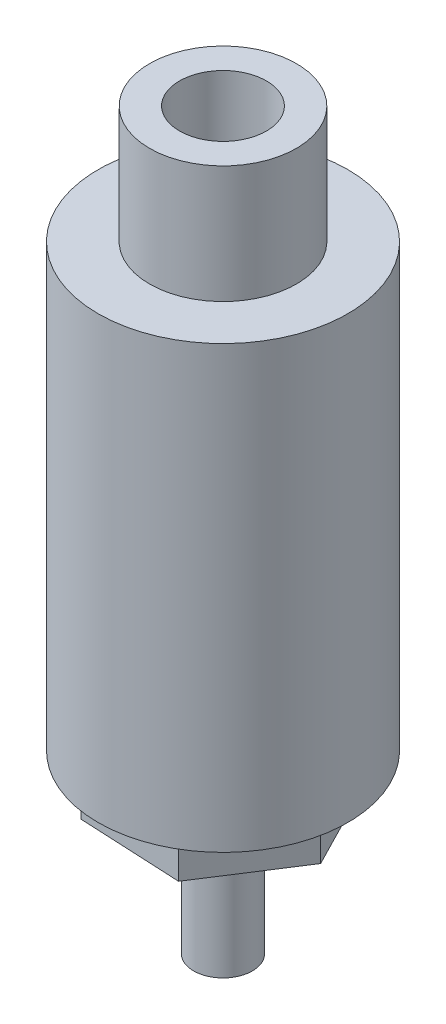
SolidWorks part; units mm, degrees
ref_plane "Front Plane" through (0, 0, 0) normal (0, 0, 1) x (1, 0, 0)
ref_plane "Top Plane" through (0, 0, 0) normal (0, 1, 0) x (1, 0, 0)
ref_plane "Right Plane" through (0, 0, 0) normal (1, 0, 0) x (0, 0, -1)
sketch "Sketch1" plane through (0, 0, 0) normal (0, 0, 1) x (1, 0, 0)
  line L0 (8.5, 0) -> (0, 0)
  line L1 (0, 0) -> (0, -30)
  line L2 (0, -30) -> (8.5, -30)
  line L3 (8.5, -30) -> (8.5, 0)
  line L4 (0, 0) -> (0, -30) construction
revolve "Revolve1" add sketch "Sketch1" angle 360 about L4
sketch "Sketch2" plane through (0, -30, 0) normal (0, -1, 0) x (1, 0, 0)
  line L0 (-3.7927, 5.8835) -> (3.1989, 6.2263)
  line L1 (3.1989, 6.2263) -> (6.9916, 0.3428)
  line L2 (6.9916, 0.3428) -> (3.7927, -5.8835)
  line L3 (3.7927, -5.8835) -> (-3.1989, -6.2263)
  line L4 (-3.1989, -6.2263) -> (-6.9916, -0.3428)
  line L5 (-6.9916, -0.3428) -> (-3.7927, 5.8835)
extrude "Boss-Extrude1" add sketch "Sketch2" along normal blind 3
sketch "Sketch3" plane through (0, 0, 0) normal (0, 1, 0) x (-1, 0, 0)
  circle A0 centre (0, 0) radius 5
extrude "Boss-Extrude2" add sketch "Sketch3" along normal blind 8
sketch "Sketch4" plane through (0, 0, 0) normal (0, 0, 1) x (1, 0, 0)
  line L0 (2, -33) -> (0, -33)
  line L1 (0, -33) -> (0, -42)
  line L2 (0, -42) -> (2, -42)
  line L3 (2, -42) -> (2, -33)
  line L4 (0, -33) -> (0, -42) construction
revolve "Revolve2" add sketch "Sketch4" angle 360 about L4
hole_wizard "Hole1" positions "Sketch6" profile "Sketch5" legacy
sketch "Sketch6" plane through (0, 8, 0) normal (0, 1, 0) x (1, 0, 0)
  point P0 (0, 0)
sketch "Sketch5" plane through (0, 8, 0) normal (1, 0, 0) x (0, 0, 1)
  line L0 (0, 0) -> (0, 15.7776)
  line L1 (0, 15.7776) -> (2.9585, 14)
  line L2 (2.9585, 14) -> (2.9585, 0)
  line L4 (2.9585, 0) -> (0, 0)
  line L6 (0, 15.7776) -> (-2.9585, 14) construction
  line L7 (0, -4.2442) -> (0, 117.3081) construction
  dimension "Diameter" = 5.917
  dimension "Depth" = 14
  dimension "Drill Angle" = 118
